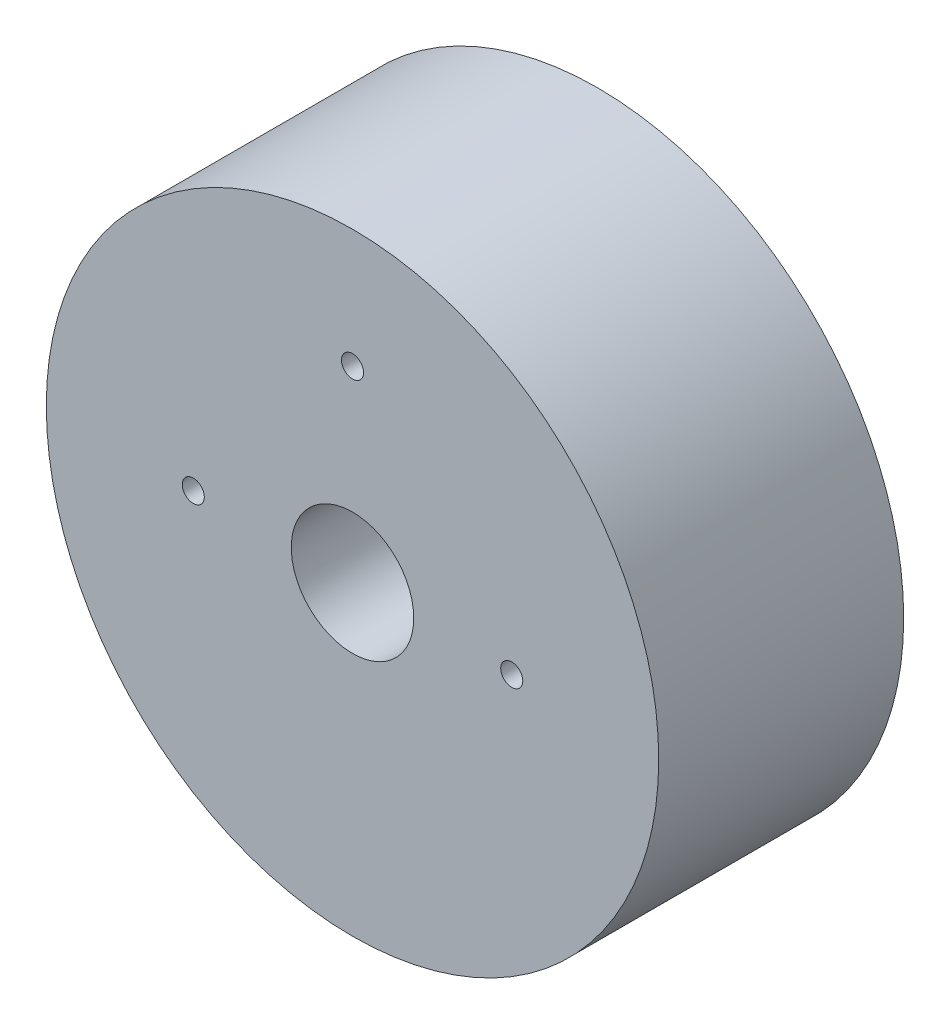
SolidWorks part; units mm, degrees
ref_plane "Front Plane" through (0, 0, 0) normal (0, 0, 1) x (1, 0, 0)
ref_plane "Top Plane" through (0, 0, 0) normal (0, 1, 0) x (1, 0, 0)
ref_plane "Right Plane" through (0, 0, 0) normal (1, 0, 0) x (0, 0, -1)
sketch "Sketch1" plane through (0, 0, 0) normal (0, 0, 1) x (1, 0, 0)
  line L0 (-28.1218, 0) -> (28.1218, 0) construction
  circle A0 centre (0, 0) radius 63.5
  circle A1 centre (-33.02, 0) radius 2.286
  circle A2 centre (33.02, 0) radius 2.286
  circle A3 centre (0, 38.862) radius 2.286
  point P6 (0, 0)
  point P10 (0, 0)
  point P11 (0, 0)
  dimension "D1" = 127
  dimension "D2" = 4.572
  dimension "D3" = 4.572
  dimension "D4" = 33.02
  dimension "D5" = 66.04
  dimension "D7" = 4.572
  dimension "D6" = 38.862
extrude "Boss-Extrude1" add sketch "Sketch1" along normal blind 50.8
sketch "Sketch2" plane through (0, 0, 50.8) normal (0, 0, 1) x (1, 0, 0)
  circle A0 centre (0, 0) radius 12.7
  dimension "D1" = 25.4
extrude "Cut-Extrude1" cut sketch "Sketch2" against normal through all
